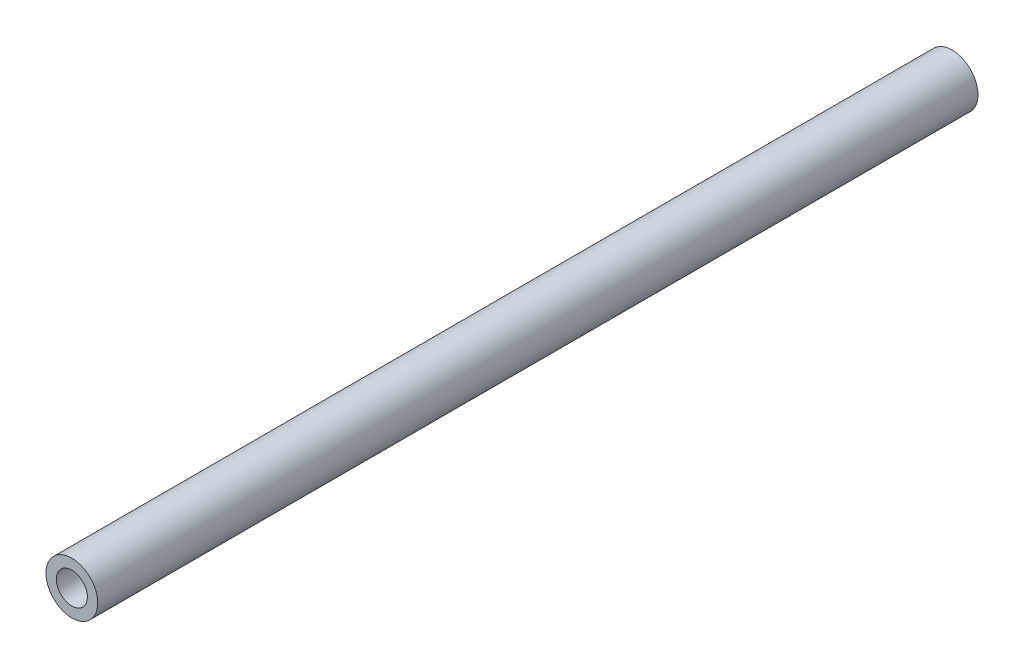
SolidWorks part; units mm, degrees
ref_plane "Front Plane" through (0, 0, 0) normal (0, 0, 1) x (1, 0, 0)
ref_plane "Top Plane" through (0, 0, 0) normal (0, 1, 0) x (1, 0, 0)
ref_plane "Right Plane" through (0, 0, 0) normal (1, 0, 0) x (0, 0, -1)
sketch "Sketch1" plane through (0, 0, 0) normal (0, 0, 1) x (1, 0, 0)
  circle A0 centre (0, 0) radius 5
  circle A1 centre (0, 0) radius 3
  dimension "D1" = 10
  dimension "D2" = 2
extrude "Boss-Extrude1" add sketch "Sketch1" along normal blind 170
